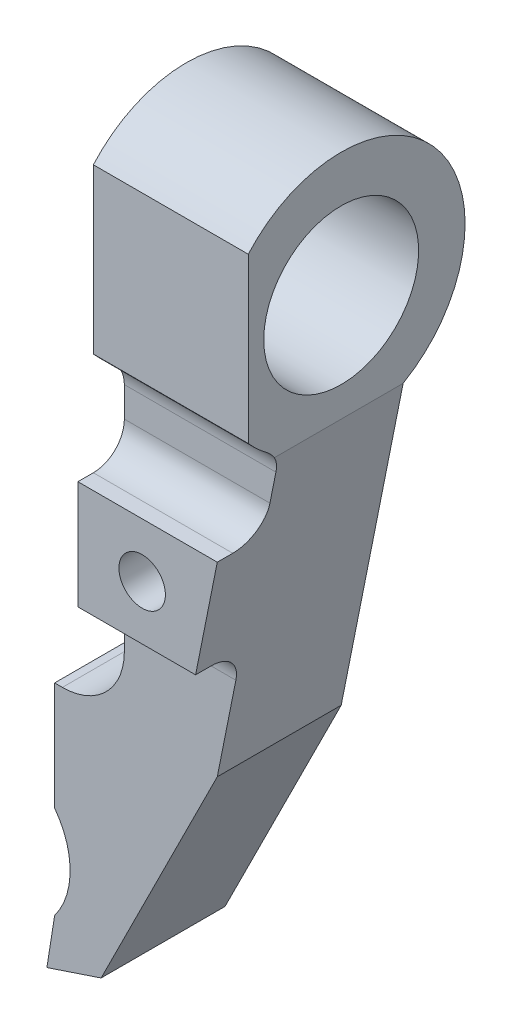
SolidWorks part; units mm, degrees
ref_plane "Plan de face" through (0, 0, 0) normal (0, 0, 1) x (1, 0, 0)
ref_plane "Plan de dessus" through (0, 0, 0) normal (0, 1, 0) x (1, 0, 0)
ref_plane "Plan de droite" through (0, 0, 0) normal (1, 0, 0) x (0, 0, -1)
sketch "Esquisse1" plane through (0, 0, 0) normal (0, 0, 1) x (1, 0, 0)
  line L0 (0, 0) -> (10, 0)
  line L1 (10, 0) -> (6, -20)
  line L2 (6, -20) -> (-1.5, -35)
  line L3 (-1.5, -35) -> (-4.5, -36)
  line L4 (-4.5, -36) -> (-4.5, -20)
  line L5 (-4.5, -20) -> (0, -20)
  line L6 (0, -20) -> (0, 0)
  point P8 (5, 0)
  dimension "D1" = 10
  dimension "D2" = 20
  dimension "D3" = 6
  dimension "D4" = 16
  dimension "D5" = 3
  dimension "D6" = 14.5
  dimension "D7" = 15
extrude "Boss.-Extru.1" add sketch "Esquisse1" along normal blind 8
fillet "Congé1" radius 4 1 edges at (0, -20, 4)
sketch "Esquisse2" plane through (0, 0, 8) normal (0, 0, 1) x (1, 0, 0)
  line L0 (-4.5, -20) -> (-4.5, -36) construction
  line L1 (-4, -20) -> (-4.5, -20) construction
  circle A0 centre (-8.5, -30) radius 5
  dimension "D1" = 10
  dimension "D2" = 4
  dimension "D3" = 10
extrude "Enlèv. mat.-Extru.1" cut sketch "Esquisse2" against normal through all
sketch "Esquisse3" plane through (0, 0, 8) normal (0, 0, 1) x (1, 0, 0)
  line L0 (-4.5, -33) -> (-5, -36.1667)
  line L1 (-5, -36.1667) -> (-4.5, -36)
  line L2 (-4.5, -36) -> (-4.5, -33)
  line L3 (-4.5, -36) -> (-1.5, -35) construction
  point P7 (-4.5, -34.5)
  dimension "D1" = 0.5
extrude "Boss.-Extru.2" add sketch "Esquisse3" against normal up to surface (8 mm away) up to face at (-0.5672, -20.7828, 0)
sketch "Esquisse4" plane through (0, 0, 0) normal (-1, 0, 0) x (0, 0, 1)
  line L0 (8, 0) -> (0, 0) construction
  line L1 (8, 0) -> (0, 0)
  arc A0 (8, 0) -> (0, 0) centre (4, 6.9282) ccw
  circle A1 centre (4, 6.9282) radius 5
  dimension "D1" = 16
  dimension "D2" = 10
extrude "Boss.-Extru.3" add sketch "Esquisse4" against normal up to vertex (10 mm away)
sketch "Esquisse5" plane through (10, 0, 0) normal (1, 0, 0) x (0, 0, -1)
  line L0 (-10, 12.2197) -> (-10, 1.6367)
  arc A0 (0, 0) -> (-8, 0) centre (-4, 6.9282) ccw construction
  dimension "D1" = 6
extrude "Enlèv. mat.-Extru.2" cut sketch "Esquisse5" against normal through all and the other way through all flip side to cut
sketch "Esquisse6" plane through (0, 0, 8) normal (0, 0, 1) x (1, 0, 0)
  line L0 (0, 0) -> (0, -16) construction
  line L1 (0, -5) -> (0, -12)
  line L2 (6, -20) -> (10, 0) construction
  line L3 (7.6, -12) -> (9, -5)
  line L4 (0, -12) -> (7.6, -12)
  line L5 (0, -5) -> (9, -5)
  dimension "D1" = 7
  dimension "D2" = 8
extrude "Boss.-Extru.4" add sketch "Esquisse6" along normal offset from surface (3 mm away) 11 up to face at (-0.6172, -20.7995, 0)
fillet "Congé2" radius 2 3 edges at (5, 0, 8) (4.5, -5, 8) (3.8, -12, 8)
sketch "Esquisse7" plane through (0, 0, 11) normal (0, 0, 1) x (1, 0, 0)
  line L0 (0, -8.5) -> (8.3, -8.5) construction
  line L1 (0, -12) -> (0, -5) construction
  line L2 (9, -5) -> (7.6, -12) construction
  circle A0 centre (4.15, -8.5) radius 1.5
  dimension "D1" = 3
extrude "Enlèv. mat.-Extru.3" cut sketch "Esquisse7" against normal through all
